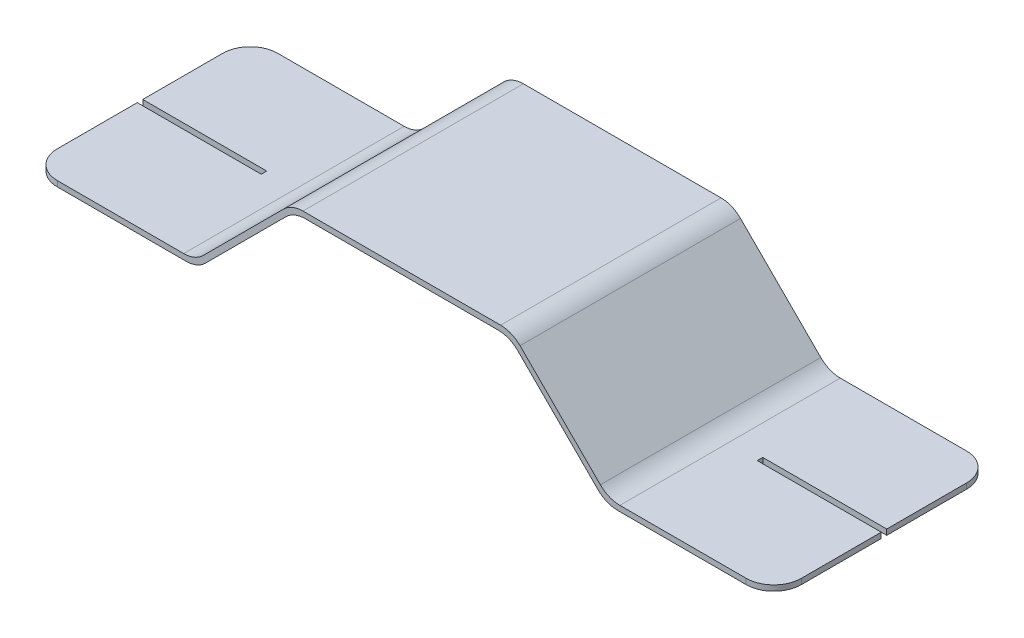
SolidWorks part; units mm, degrees
ref_plane "Front Plane" through (0, 0, 0) normal (0, 0, 1) x (1, 0, 0)
ref_plane "Top Plane" through (0, 0, 0) normal (0, 1, 0) x (1, 0, 0)
ref_plane "Right Plane" through (0, 0, 0) normal (1, 0, 0) x (0, 0, -1)
sketch "Sketch1" plane through (0, 0, 0) normal (0, 0, 1) x (1, 0, 0)
  line L0 (0, 0) -> (8, 0)
  line L1 (8, 0) -> (11.5, -3.5)
  line L2 (11.5, -3.5) -> (17.5, -3.5)
  line L3 (0, 0) -> (-3.5, -3.5)
  line L4 (-3.5, -3.5) -> (-9.5, -3.5)
  line L5 (-3.4172, -3.7) -> (-9.5, -3.7)
  line L6 (0.0828, -0.2) -> (-3.4172, -3.7)
  line L7 (0.0828, -0.2) -> (7.9172, -0.2)
  line L8 (7.9172, -0.2) -> (11.4172, -3.7)
  line L9 (11.4172, -3.7) -> (17.5, -3.7)
  line L10 (-9.5, -3.5) -> (-9.5, -3.7)
  line L11 (17.5, -3.5) -> (17.5, -3.7)
  dimension "D1" = 8
  dimension "D2" = 3.5
  dimension "D3" = 3.5
  dimension "D4" = 3.5
  dimension "D5" = 6
  dimension "D6" = 0.2
extrude "Boss-Extrude1" add sketch "Sketch1" along normal blind 8
sketch "Sketch2" plane through (0, 0, 0) normal (-0.7071, 0.7071, 0) x (0, 0, 1)
  line L0 (8, 0) -> (0, 0) construction
  circle A0 centre (2.25, -2.5) radius 1.1906
  circle A1 centre (5.75, -2.5) radius 1.1906
  point P9 (4, 0)
  dimension "D1" = 2.3813
  dimension "D2" = 2.5
  dimension "D3" = 3.5
  dimension "D4" = 1.75
extrude "Cut-Extrude1" cut sketch "Sketch2" against normal through all
fillet "Fillet1" radius 1 8 edges at (7.9172, -0.2, 4) (11.4172, -3.7, 4) (-3.4172, -3.7, 4) (0.0828, -0.2, 4) (11.5, -3.5, 4) (8, 0, 4) (0, 0, 4) (-3.5, -3.5, 4)
fillet "Fillet2" radius 1 4 edges at (17.5, -3.6, 0) (17.5, -3.6, 8) (-9.5, -3.6, 0) (-9.5, -3.6, 8)
sketch "Sketch3" plane through (0, -3.5, 0) normal (0, 1, 0) x (1, 0, 0)
  line L0 (-9.5, -7) -> (-9.5, -1) construction
  line L1 (-9.5, -3.9) -> (-5, -3.9)
  line L2 (-9.5, -3.9) -> (-9.5, -4.1)
  line L3 (-9.5, -4.1) -> (-5, -4.1)
  line L4 (-5, -3.9) -> (-5, -4.1)
  point P6 (-9.5, -4)
  dimension "D1" = 0.2
  dimension "D2" = 4.5
extrude "Cut-Extrude2" cut sketch "Sketch3" against normal blind 10
ref_plane "Plane1" through (4, 0, 0) normal (1, 0, 0) x (0, 0, -1)
mirror "Mirror1" about plane through (4, 0, 0) normal (1, 0, 0) of "Cut-Extrude2"
equation "\"D4@Sketch2\"=3.5/2"
